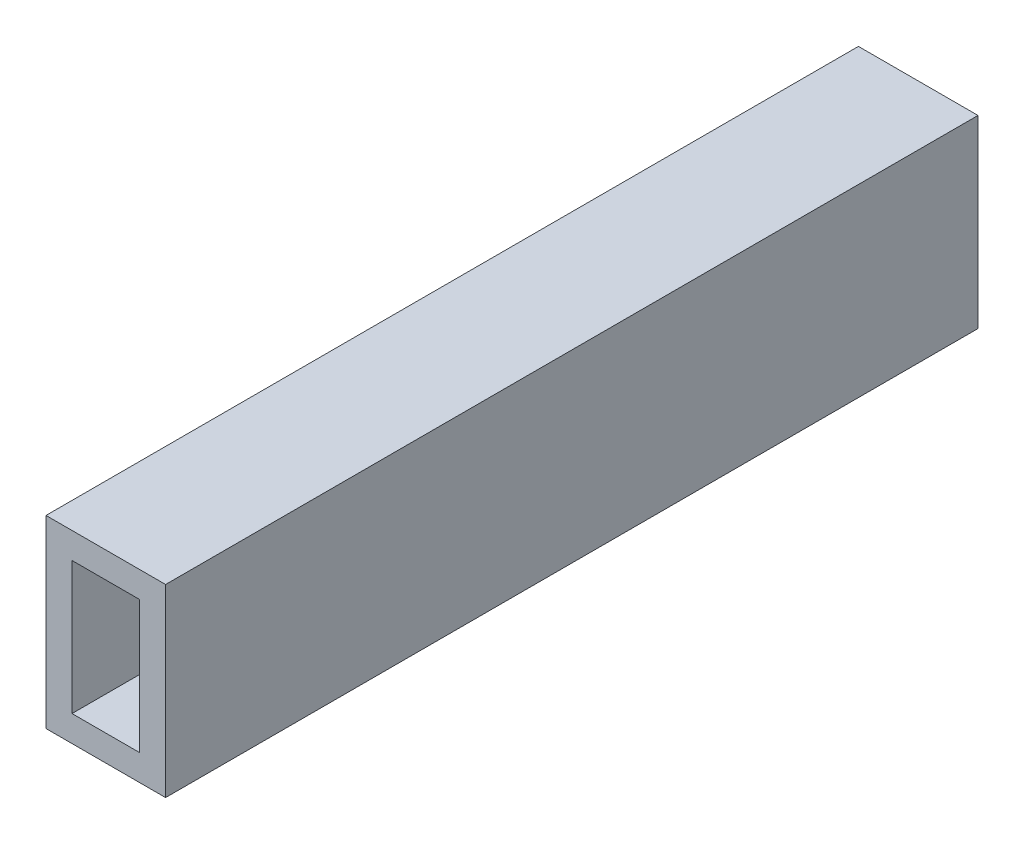
SolidWorks part; units mm, degrees
ref_plane "Front Plane" through (0, 0, 0) normal (0, 0, 1) x (1, 0, 0)
ref_plane "Top Plane" through (0, 0, 0) normal (0, 1, 0) x (1, 0, 0)
ref_plane "Right Plane" through (0, 0, 0) normal (1, 0, 0) x (0, 0, -1)
sketch "Sketch1" plane through (0, 0, 0) normal (0, 0, 1) x (1, 0, 0)
  line L1 (1.3, -2.55) -> (-1.3, -2.55)
  line L2 (1.3, -2.55) -> (1.3, 2.55)
  line L3 (1.3, 2.55) -> (-1.3, 2.55)
  line L4 (-1.3, -2.55) -> (-1.3, 2.55)
  line L5 (1.3, -2.55) -> (-1.3, 2.55) construction
  line L6 (1.3, 2.55) -> (-1.3, -2.55) construction
  line L7 (-2.3, -3.55) -> (2.3, -3.55)
  line L8 (-2.3, -3.55) -> (-2.3, 3.55)
  line L9 (-2.3, 3.55) -> (2.3, 3.55)
  line L10 (2.3, -3.55) -> (2.3, 3.55)
  line L11 (-2.3, -3.55) -> (2.3, 3.55) construction
  line L12 (-2.3, 3.55) -> (2.3, -3.55) construction
  point P0 (0, 0)
  point P6 (0, 0)
  point P11 (0, 0)
  dimension "D1" = 1
  dimension "D2" = 1
  dimension "D3" = 5.1
  dimension "D4" = 2.6
extrude "Boss-Extrude1" add sketch "Sketch1" along normal blind 31.25
